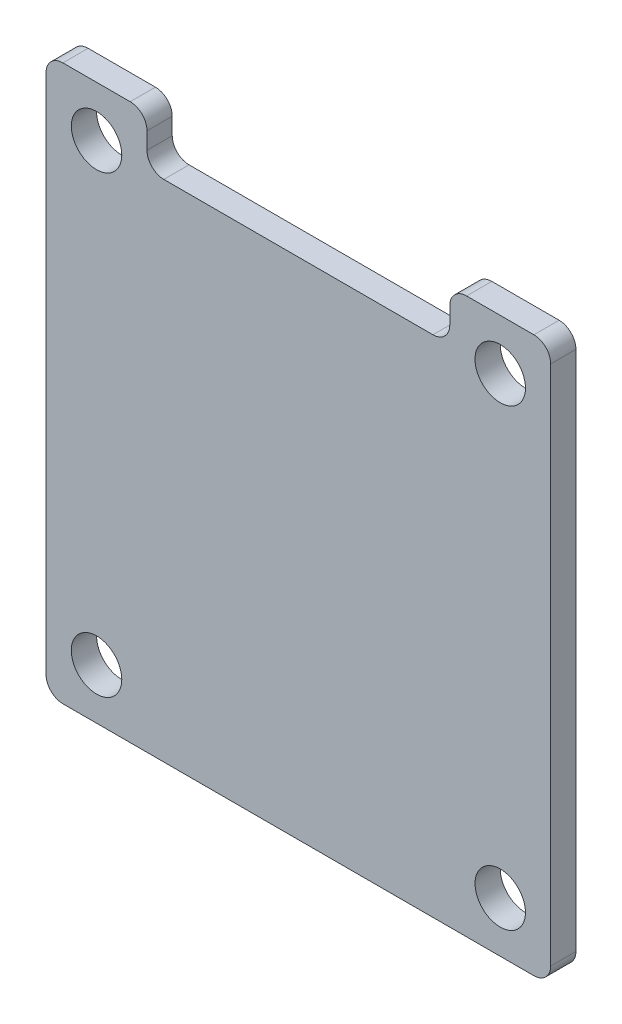
SolidWorks part; units mm, degrees
ref_plane "正面" through (0, 0, 0) normal (0, 0, 1) x (1, 0, 0)
ref_plane "平面" through (0, 0, 0) normal (0, 1, 0) x (1, 0, 0)
ref_plane "右側面" through (0, 0, 0) normal (1, 0, 0) x (0, 0, -1)
sketch "ｽｹｯﾁ1" plane through (0, 0, 0) normal (0, 0, 1) x (1, 0, 0)
  line L1 (-15, 15) -> (15, 15)
  line L2 (-15, 15) -> (-15, -15)
  line L3 (-15, -15) -> (15, -15)
  line L4 (15, 15) -> (15, -15)
  line L5 (-15, 15) -> (-9, 15)
  line L6 (-15, 15) -> (-15, 18)
  line L7 (-15, 18) -> (-9, 18)
  line L8 (-9, 15) -> (-9, 18)
  line L9 (15, 15) -> (9, 15)
  line L10 (15, 15) -> (15, 18)
  line L11 (15, 18) -> (9, 18)
  line L12 (9, 15) -> (9, 18)
  circle A0 centre (-12, 15) radius 1.5
  circle A1 centre (12, 15) radius 1.5
  circle A2 centre (-12, -12) radius 1.5
  circle A3 centre (12, -12) radius 1.4996
  point P11 (-12, 15)
  point P12 (12, 15)
  dimension "D9" = 3
  dimension "D10" = 3
  dimension "D15" = 3
  dimension "D18" = 2.9992
  dimension "D1" = 30
  dimension "D2" = 30
  dimension "D3" = 15
  dimension "D4" = 15
  dimension "D5" = 3
  dimension "D6" = 3
  dimension "D7" = 6
  dimension "D8" = 6
  dimension "D11" = 3
  dimension "D12" = 3
  dimension "D13" = 3
  dimension "D14" = 3
  dimension "D16" = 3
  dimension "D17" = 3
extrude "ﾎﾞｽ - 押し出し1" add sketch "ｽｹｯﾁ1" along normal blind 1.5 contours A1 L1 A0 L2 L3 L4 A3 A2 | A0 L1 L8 L7 L6 | A1 L1 L10 L11 L12
fillet "ﾌｨﾚｯﾄ2" radius 1 8 edges at (-15, 18, 0.75) (-9, 18, 0.75) (-9, 15, 0.75) (9, 15, 0.75) (9, 18, 0.75) (15, 18, 0.75) (15, -15, 0.75) (-15, -15, 0.75)
